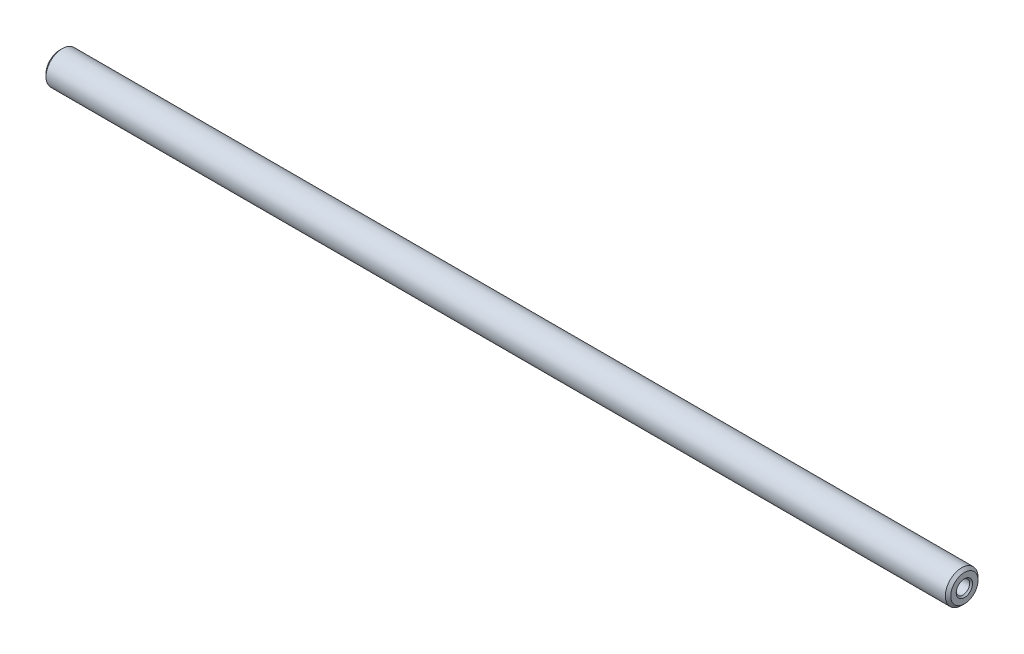
SolidWorks part; units mm, degrees
ref_plane "Front Plane" through (0, 0, 0) normal (0, 0, 1) x (1, 0, 0)
ref_plane "Top Plane" through (0, 0, 0) normal (0, 1, 0) x (1, 0, 0)
ref_plane "Right Plane" through (0, 0, 0) normal (1, 0, 0) x (0, 0, -1)
ref_plane "Plane1" through (0, 0, 0) normal (0, 0, -1) x (-1, 0, 0)
sketch "Sketch1" plane through (0, 0, 0) normal (0, 0, -1) x (-1, 0, 0)
  line L0 (-155.2099, 1.2295) -> (-154.5, 0)
  line L1 (-154.5, 0) -> (-11.5, 0)
  line L2 (-11.5, 0) -> (-10.7901, 1.2295)
  line L3 (-10.7901, 1.2295) -> (-0.2705, 1.2295)
  line L4 (-0.2705, 1.2295) -> (0, 1.5)
  line L5 (0, 1.5) -> (0, 2.5)
  line L6 (0, 2.5) -> (-0.5, 3)
  line L7 (-0.5, 3) -> (-165.5, 3)
  line L8 (-165.5, 3) -> (-166, 2.5)
  line L9 (-166, 2.5) -> (-166, 1.5)
  line L10 (-166, 1.5) -> (-165.7295, 1.2295)
  line L11 (-165.7295, 1.2295) -> (-155.2099, 1.2295)
  line L12 (-166, 0) -> (0, 0) construction
revolve "Revolve1" add sketch "Sketch1" angle 360 about L12
